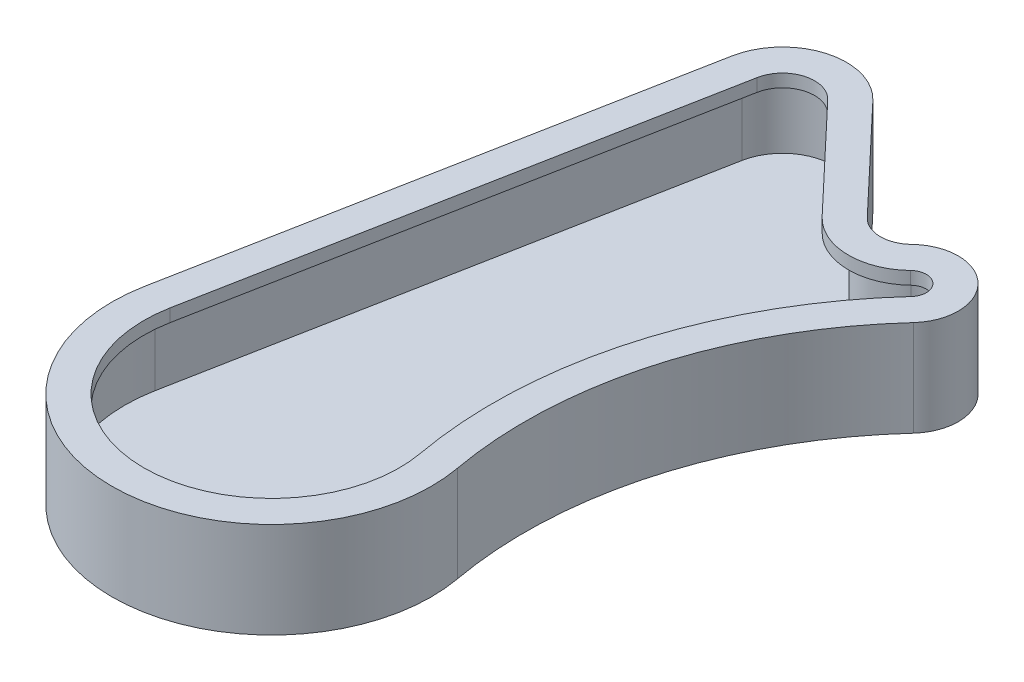
SolidWorks part; units mm, degrees
ref_plane "Front Plane" through (0, 0, 0) normal (0, 0, 1) x (1, 0, 0)
ref_plane "Top Plane" through (0, 0, 0) normal (0, 1, 0) x (1, 0, 0)
ref_plane "Right Plane" through (0, 0, 0) normal (1, 0, 0) x (0, 0, -1)
sketch "Sketch1" plane through (0, 0, 0) normal (0, 1, 0) x (1, 0, 0)
  line L0 (0, 0) -> (0, 80) construction
  line L1 (-24.5566, 4.6875) -> (-9.8226, 81.875)
  line L2 (7.2643, 86.8724) -> (22.6932, 70.5638)
  arc A0 (-24.5566, 4.6875) -> (24.5957, 4.4778) centre (0, 0) ccw
  arc A1 (7.2643, 86.8724) -> (-9.8226, 81.875) centre (0, 80) ccw
  arc A2 (40.5391, 59.9435) -> (29.7952, 70.4) centre (35, 65) ccw
  arc A3 (24.5957, 4.4778) -> (40.5391, 59.9435) centre (88.5446, 16.1202) cw
  arc A4 (22.6932, 70.5638) -> (29.7952, 70.4) centre (26.3253, 74) ccw
  dimension "D1" = 50
  dimension "D2" = 20
  dimension "D3" = 115
  dimension "D4" = 15
  dimension "D5" = 97.5
  dimension "D6" = 67.5
  dimension "D7" = 65
  dimension "D8" = 5
  dimension "D9" = 21
extrude "Boss-Extrude2" add sketch "Sketch1" along normal blind 15
sketch "Sketch2" plane through (0, 15, 0) normal (0, 1, 0) x (1, 0, 0)
  line L4 (21.2403, 69.1893) -> (5.8114, 85.4979)
  line L5 (-7.8581, 81.5) -> (-22.5921, 4.3125)
  line L6 (21.2403, 69.1893) -> (5.8114, 85.4979)
  line L7 (-7.8581, 81.5) -> (-22.5921, 4.3125)
  arc A10 (-22.5921, 4.3125) -> (22.6281, 4.1196) centre (0, 0) ccw
  arc A11 (39.062, 61.2919) -> (22.6281, 4.1196) centre (88.5446, 16.1202) ccw
  arc A12 (39.062, 61.2919) -> (31.1831, 68.96) centre (35, 65) ccw
  arc A13 (21.2403, 69.1893) -> (31.1831, 68.96) centre (26.3253, 74) ccw
  arc A14 (5.8114, 85.4979) -> (-7.8581, 81.5) centre (0, 80) ccw
  arc A15 (-22.5921, 4.3125) -> (22.6281, 4.1196) centre (0, 0) ccw
  arc A16 (39.062, 61.2919) -> (22.6281, 4.1196) centre (88.5446, 16.1202) ccw
  arc A17 (39.062, 61.2919) -> (31.1831, 68.96) centre (35, 65) ccw
  arc A18 (21.2403, 69.1893) -> (31.1831, 68.96) centre (26.3253, 74) ccw
  arc A19 (5.8114, 85.4979) -> (-7.8581, 81.5) centre (0, 80) ccw
  dimension "D1" = 2
extrude "Cut-Extrude1" cut sketch "Sketch2" against normal blind 13
sketch "Sketch3" plane through (0, 15, 0) normal (0, 1, 0) x (1, 0, 0)
  line L4 (19.061, 67.1276) -> (3.6321, 83.4362)
  line L5 (-4.9113, 80.9375) -> (-19.6453, 3.75)
  line L6 (19.061, 67.1276) -> (3.6321, 83.4362)
  line L7 (-4.9113, 80.9375) -> (-19.6453, 3.75)
  line L8 (22.6932, 70.5638) -> (7.2643, 86.8724)
  line L9 (-9.8226, 81.875) -> (-24.5566, 4.6875)
  line L10 (22.6932, 70.5638) -> (7.2643, 86.8724)
  line L11 (-9.8226, 81.875) -> (-24.5566, 4.6875)
  arc A10 (-19.6453, 3.75) -> (19.6766, 3.5823) centre (0, 0) ccw
  arc A11 (36.8464, 63.3145) -> (19.6766, 3.5823) centre (88.5446, 16.1202) ccw
  arc A12 (36.8464, 63.3145) -> (33.2651, 66.8) centre (35, 65) ccw
  arc A13 (19.061, 67.1276) -> (33.2651, 66.8) centre (26.3253, 74) ccw
  arc A14 (3.6321, 83.4362) -> (-4.9113, 80.9375) centre (0, 80) ccw
  arc A15 (-19.6453, 3.75) -> (19.6766, 3.5823) centre (0, 0) ccw
  arc A16 (36.8464, 63.3145) -> (19.6766, 3.5823) centre (88.5446, 16.1202) ccw
  arc A17 (36.8464, 63.3145) -> (33.2651, 66.8) centre (35, 65) ccw
  arc A18 (19.061, 67.1276) -> (33.2651, 66.8) centre (26.3253, 74) ccw
  arc A19 (3.6321, 83.4362) -> (-4.9113, 80.9375) centre (0, 80) ccw
  arc A20 (-24.5566, 4.6875) -> (24.5957, 4.4778) centre (0, 0) ccw
  arc A21 (40.5391, 59.9435) -> (24.5957, 4.4778) centre (88.5446, 16.1202) ccw
  arc A22 (40.5391, 59.9435) -> (29.7952, 70.4) centre (35, 65) ccw
  arc A23 (22.6932, 70.5638) -> (29.7952, 70.4) centre (26.3253, 74) ccw
  arc A24 (7.2643, 86.8724) -> (-9.8226, 81.875) centre (0, 80) ccw
  arc A25 (-24.5566, 4.6875) -> (24.5957, 4.4778) centre (0, 0) ccw
  arc A26 (40.5391, 59.9435) -> (24.5957, 4.4778) centre (88.5446, 16.1202) ccw
  arc A27 (40.5391, 59.9435) -> (29.7952, 70.4) centre (35, 65) ccw
  arc A28 (22.6932, 70.5638) -> (29.7952, 70.4) centre (26.3253, 74) ccw
  arc A29 (7.2643, 86.8724) -> (-9.8226, 81.875) centre (0, 80) ccw
  dimension "D1" = 5
  dimension "D2" = 0
extrude "Boss-Extrude3" add sketch "Sketch3" against normal blind 2
